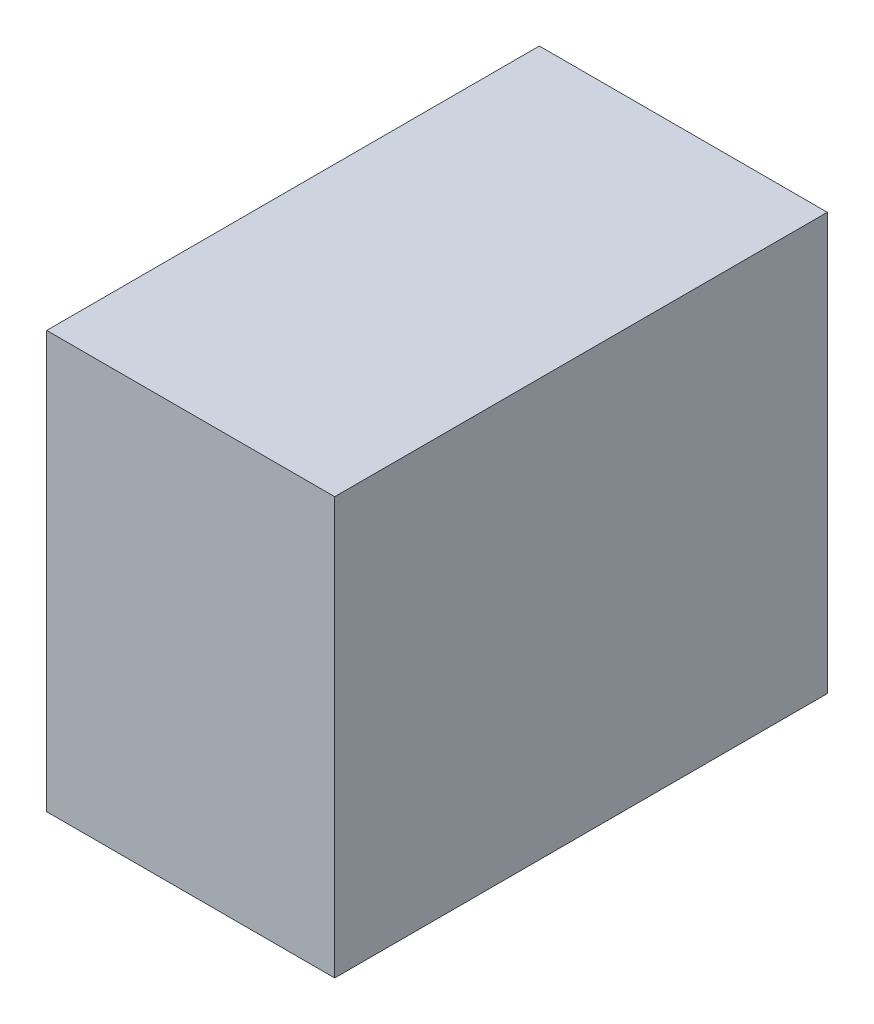
SolidWorks part; units mm, degrees
ref_plane "Front Plane" through (0, 0, 0) normal (0, 0, 1) x (1, 0, 0)
ref_plane "Top Plane" through (0, 0, 0) normal (0, 1, 0) x (1, 0, 0)
ref_plane "Right Plane" through (0, 0, 0) normal (1, 0, 0) x (0, 0, -1)
sketch "Sketch1" plane through (0, 0, 0) normal (0, 1, 0) x (1, 0, 0)
  line L1 (-69.85, 82.55) -> (69.85, 82.55)
  line L2 (-69.85, 82.55) -> (-69.85, -82.55)
  line L3 (-69.85, -82.55) -> (69.85, -82.55)
  line L4 (69.85, 82.55) -> (69.85, -82.55)
  line L5 (-69.85, 82.55) -> (69.85, -82.55) construction
  line L6 (-69.85, -82.55) -> (69.85, 82.55) construction
  point P0 (0, 0)
  dimension "D1" = 165.1
  dimension "D2" = 139.7
extrude "Boss-Extrude4" add sketch "Sketch1" along normal mid plane 96.52
move or copy body "Body-Move/Copy1" bodies to move or copy 104 copy no rotation origin (0, 0, 0) rotation axis (0, 0, 1) rotation angle 90
